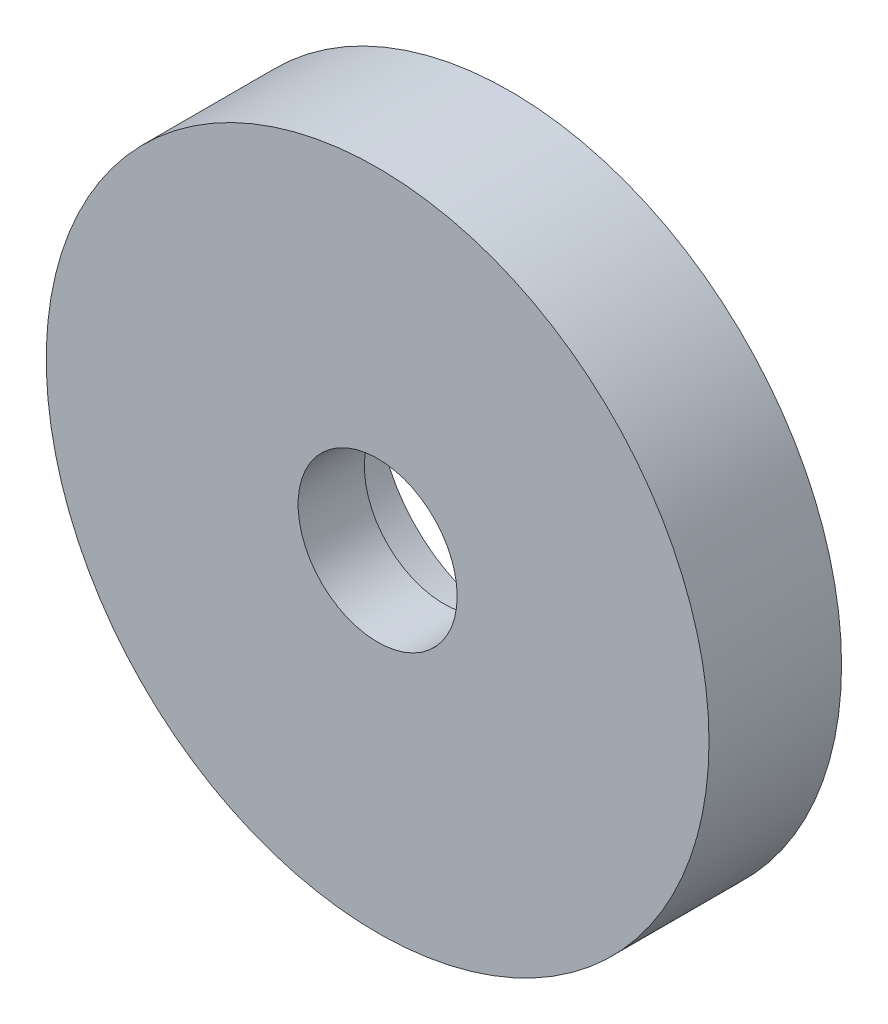
SolidWorks part; units mm, degrees
ref_plane "Front Plane" through (0, 0, 0) normal (0, 0, 1) x (1, 0, 0)
ref_plane "Top Plane" through (0, 0, 0) normal (0, 1, 0) x (1, 0, 0)
ref_plane "Right Plane" through (0, 0, 0) normal (1, 0, 0) x (0, 0, -1)
sketch "Sketch2" plane through (0, 0, 0) normal (0, 0, 1) x (1, 0, 0)
  circle A0 centre (0, 0) radius 25
  dimension "D1" = 50
extrude "Boss-Extrude1" add sketch "Sketch2" along normal blind 10
sketch "Sketch3" plane through (0, 0, 10) normal (0, 0, 1) x (1, 0, 0)
  circle A0 centre (0, 0) radius 6
  dimension "D1" = 12
extrude "Cut-Extrude1" cut sketch "Sketch3" against normal blind 5
sketch "Sketch4" plane through (0, 0, 0) normal (0, 0, -1) x (-1, 0, 0)
  circle A0 centre (0, 0) radius 10
  dimension "D1" = 20
extrude "Cut-Extrude2" cut sketch "Sketch4" against normal blind 5
